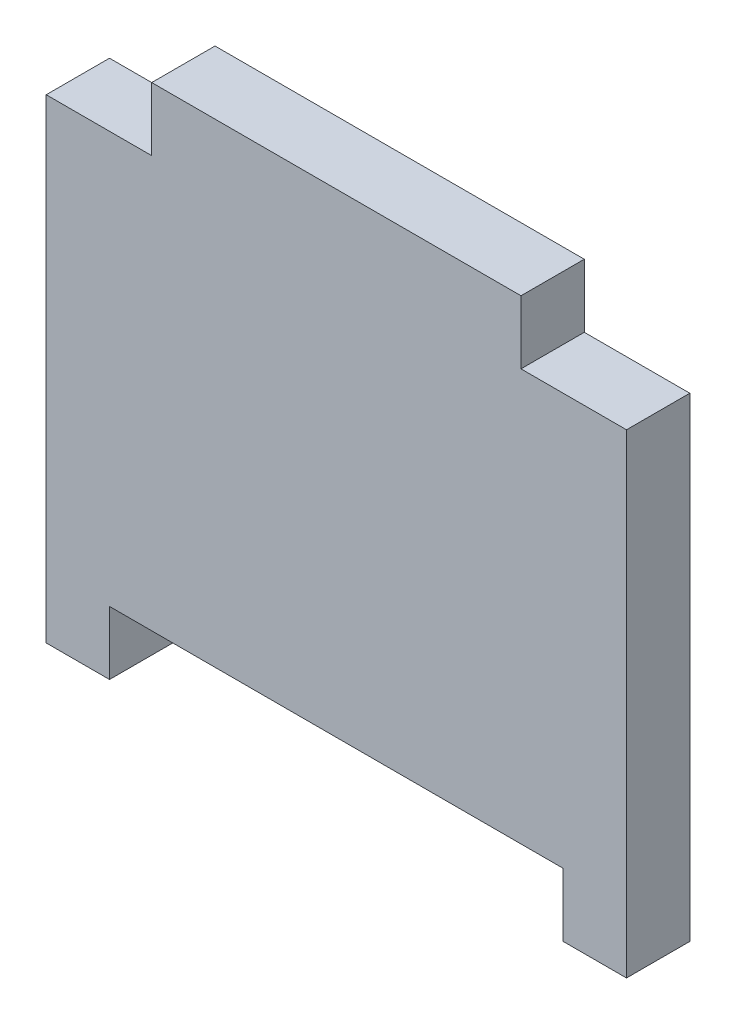
SolidWorks part; units mm, degrees
ref_plane "Front Plane" through (0, 0, 0) normal (0, 0, 1) x (1, 0, 0)
ref_plane "Top Plane" through (0, 0, 0) normal (0, 1, 0) x (1, 0, 0)
ref_plane "Right Plane" through (0, 0, 0) normal (1, 0, 0) x (0, 0, -1)
sketch "Sketch1" plane through (0, 0, 0) normal (0, 0, 1) x (1, 0, 0)
  line L0 (-6, 0) -> (0, 0)
  line L1 (-55, 51) -> (0, 51)
  line L2 (-55, 51) -> (-55, 0)
  line L3 (-55, 0) -> (-49, 0)
  line L4 (0, 51) -> (0, 0)
  line L6 (-49, 0) -> (-49, 6)
  line L7 (-49, 6) -> (-6, 6)
  line L8 (-6, 0) -> (-6, 6)
  dimension "D1" = 55
  dimension "D2" = 51
  dimension "D3" = 6
  dimension "D4" = 6
  dimension "D5" = 6
extrude "Boss-Extrude1" add sketch "Sketch1" along normal blind 6
sketch "Sketch2" plane through (0, 0, 6) normal (0, 0, 1) x (1, 0, 0)
  line L1 (-55, 51) -> (-45, 51)
  line L2 (-55, 51) -> (-55, 45)
  line L3 (-55, 45) -> (-45, 45)
  line L4 (-45, 51) -> (-45, 45)
  line L5 (0, 51) -> (-10, 51)
  line L6 (0, 51) -> (0, 45)
  line L7 (0, 45) -> (-10, 45)
  line L8 (-10, 51) -> (-10, 45)
  dimension "D1" = 6
  dimension "D2" = 10
  dimension "D3" = 6
  dimension "D4" = 10
extrude "Cut-Extrude1" cut sketch "Sketch2" against normal blind 6
